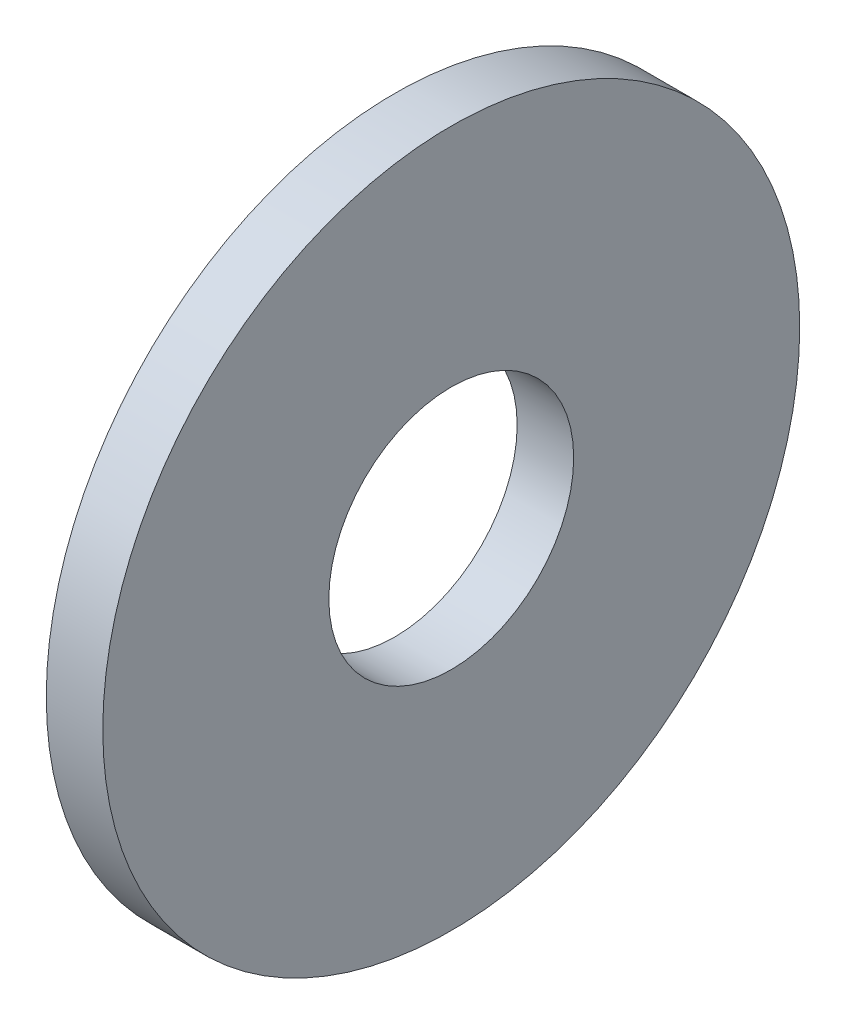
SolidWorks part; units mm, degrees
ref_plane "Plane1" through (0, 0, 0) normal (0, 0, 1) x (1, 0, 0)
ref_plane "Plane2" through (0, 0, 0) normal (0, 1, 0) x (1, 0, 0)
ref_plane "Plane3" through (0, 0, 0) normal (1, 0, 0) x (0, 0, -1)
sketch "Sketch1" plane through (0, 0, 0) normal (0, 0, 1) x (1, 0, 0)
  line L0 (-34.925, 0) -> (9.525, 0) construction
  line L1 (0, 6.5) -> (0, 18.5)
  line L2 (0, 18.5) -> (-3, 18.5)
  line L3 (-3, 18.5) -> (-3, 6.5)
  line L4 (-3, 6.5) -> (0, 6.5)
  dimension "Thickness" = 3
  dimension "Inside_dia" = 13
  dimension "Outside_dia" = 37
revolve "Base-Revolve" add sketch "Sketch1" angle 360 about L0
